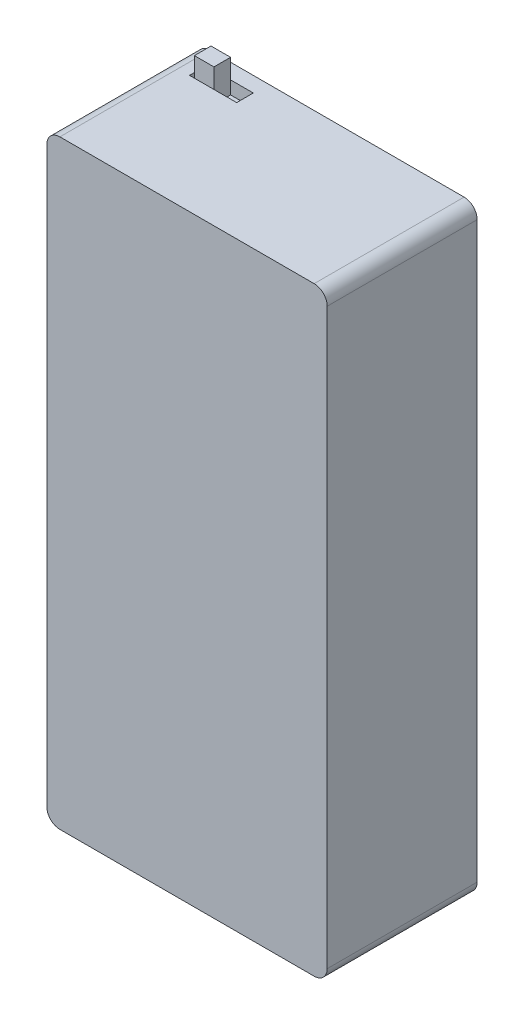
SolidWorks part; units mm, degrees
ref_plane "Front Plane" through (0, 0, 0) normal (0, 0, 1) x (1, 0, 0)
ref_plane "Top Plane" through (0, 0, 0) normal (0, 1, 0) x (1, 0, 0)
ref_plane "Right Plane" through (0, 0, 0) normal (1, 0, 0) x (0, 0, -1)
sketch "Sketch1" plane through (0, 0, 0) normal (0, 0, 1) x (1, 0, 0)
  line L1 (2, 0) -> (41, 0)
  line L2 (0, 2) -> (0, 90)
  line L3 (2, 92) -> (41, 92)
  line L4 (43, 2) -> (43, 90)
  arc A0 (43, 2) -> (41, 0) centre (41, 2) cw
  arc A1 (0, 2) -> (2, 0) centre (2, 2) ccw
  arc A2 (43, 90) -> (41, 92) centre (41, 90) ccw
  arc A3 (0, 90) -> (2, 92) centre (2, 90) cw
  point P7 (43, 0)
  point P10 (0, 0)
  point P15 (0, 92)
  dimension "D3" = 2
  dimension "D1" = 43
  dimension "D2" = 92
extrude "Boss-Extrude1" add sketch "Sketch1" along normal blind 23
sketch "Sketch2" plane through (0, 92, 0) normal (0, 1, 0) x (1, 0, 0)
  line L1 (3.7716, -2.3424) -> (11.0053, -2.3424)
  line L2 (3.7716, -2.3424) -> (3.7716, -4.892)
  line L3 (3.7716, -4.892) -> (11.0053, -4.892)
  line L4 (11.0053, -2.3424) -> (11.0053, -4.892)
extrude "Cut-Extrude1" cut sketch "Sketch2" against normal blind 2
sketch "Sketch3" plane through (0, 90, 0) normal (0, 1, 0) x (1, 0, 0)
  line L0 (11.0053, -2.3424) -> (3.7716, -2.3424) construction
  line L1 (4.5197, -2.3424) -> (7.5197, -2.3424)
  line L2 (4.5197, -2.3424) -> (4.5197, -4.892)
  line L3 (4.5197, -4.892) -> (7.5197, -4.892)
  line L4 (7.5197, -2.3424) -> (7.5197, -4.892)
  line L5 (3.7716, -4.892) -> (11.0053, -4.892) construction
  dimension "D1" = 3
extrude "Boss-Extrude2" add sketch "Sketch3" along normal blind 5
